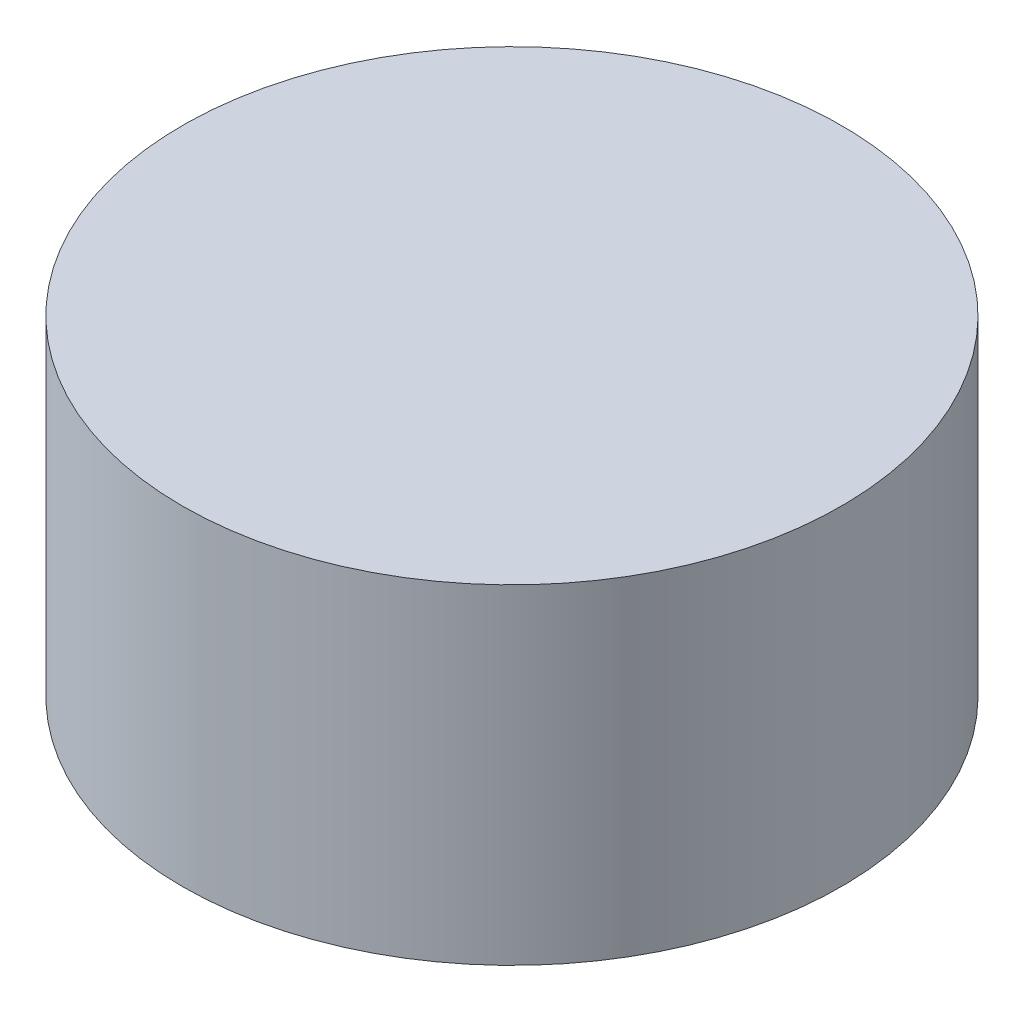
SolidWorks part; units mm, degrees
ref_plane "前视基准面" through (0, 0, 0) normal (0, 0, 1) x (1, 0, 0)
ref_plane "上视基准面" through (0, 0, 0) normal (0, 1, 0) x (1, 0, 0)
ref_plane "右视基准面" through (0, 0, 0) normal (1, 0, 0) x (0, 0, -1)
sketch "草图1" plane through (0, 0, 0) normal (0, 1, 0) x (1, 0, 0)
  circle A0 centre (0, 0) radius 3
extrude "凸台-拉伸1" add sketch "草图1" along normal blind 3
